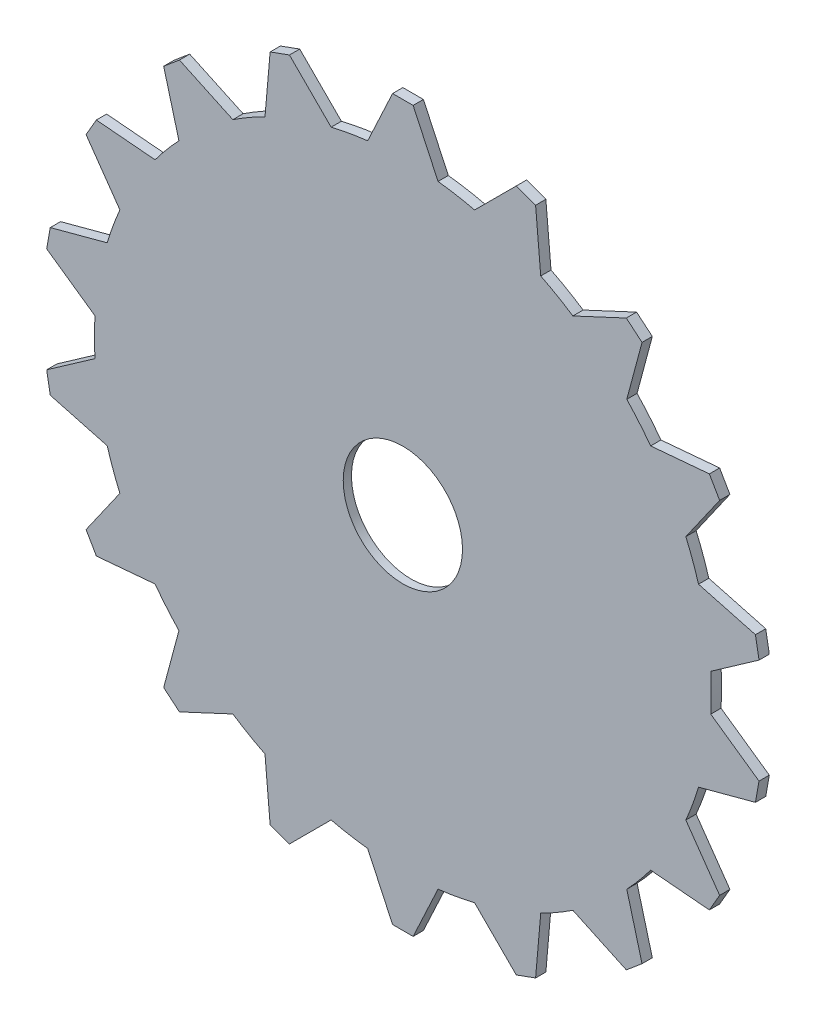
SolidWorks part; units mm, degrees
ref_plane "Front Plane" through (0, 0, 0) normal (0, 0, 1) x (1, 0, 0)
ref_plane "Top Plane" through (0, 0, 0) normal (0, 1, 0) x (1, 0, 0)
ref_plane "Right Plane" through (0, 0, 0) normal (1, 0, 0) x (0, 0, -1)
sketch "Sketch1" plane through (0, 0, 0) normal (0, 0, 1) x (1, 0, 0)
  circle A0 centre (0, 0) radius 38.1
  dimension "D1" = 76.2
extrude "Boss-Extrude1" add sketch "Sketch1" along normal blind 1.27
sketch "Sketch2" plane through (0, 0, 1.27) normal (0, 0, 1) x (1, 0, 0)
  line L0 (0, 38.1) -> (0, 44.45) construction
  line L1 (-1.27, 44.45) -> (1.27, 44.45)
  line L2 (1.27, 44.45) -> (4.3471, 37.8512)
  line L3 (-1.27, 44.45) -> (-4.3471, 37.8512)
  line L4 (70, -22.38) -> (63.4012, -19.3029)
  line L5 (70, -22.38) -> (70, -24.92)
  line L6 (70, -24.92) -> (63.4012, -27.9971)
  line L7 (3.17, -93.65) -> (6.2471, -87.0512)
  line L8 (3.17, -93.65) -> (0.63, -93.65)
  line L9 (0.63, -93.65) -> (-2.4471, -87.0512)
  line L10 (-68.1, -26.82) -> (-61.5012, -29.8971)
  line L11 (-68.1, -26.82) -> (-68.1, -24.28)
  line L12 (-68.1, -24.28) -> (-61.5012, -21.2029)
  circle A0 centre (0, 0) radius 38.1 construction
  arc A1 (4.3471, 37.8512) -> (-4.3471, 37.8512) centre (0, 0) ccw
  point P25 (0.95, -24.6)
  circle M1 centre (0, 0) radius 38.1
  dimension "D1" = 1.27
  dimension "D2" = 4
  dimension "D3" = 6.35
  dimension "D4" = 65
extrude "Boss-Extrude2" add sketch "Sketch2" against normal blind 1.27 contours L12 L11 L10 M1 | A1 L0 L1 L3 | L0 L2 L1 M1 | L6 L5 L4 M1 | L9 L8 L7 M1
sketch "Sketch3" plane through (0, 0, 0) normal (0, 0, -1) x (-1, 0, 0)
  circle A0 centre (0, 0) radius 7.366
  dimension "D1" = 14.732
extrude "Cut-Extrude1" cut sketch "Sketch3" against normal blind 10
pattern_circular "CirPattern1" count 19 every 20 about axis through (0, 0, 0) along (0, 0, 1) of "Boss-Extrude2"
sketch "Sketch4" plane through (0, 0, 0) normal (0, 0, -1) x (-1, 0, 0)
  circle A0 centre (0, 0) radius 25.4
  dimension "D1" = 50.8
extrude "Cut-Extrude2" cut sketch "Sketch4" against normal blind 0.254
